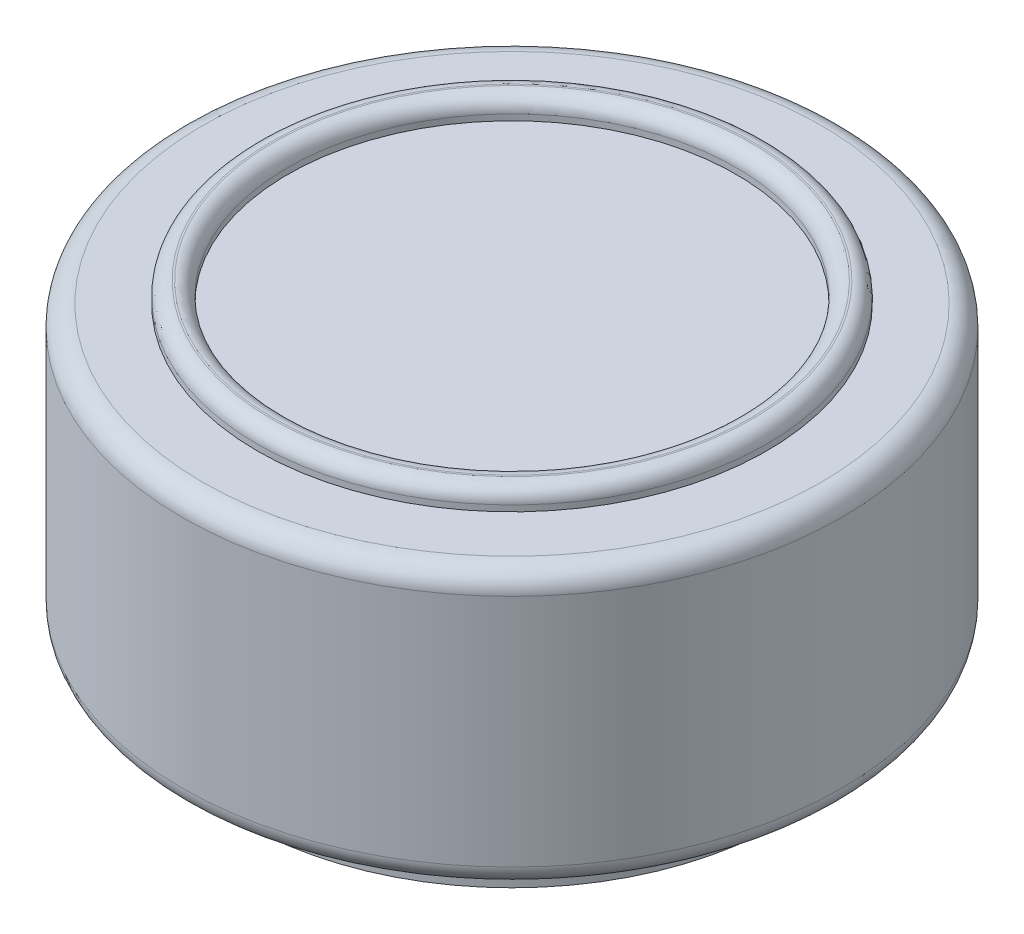
SolidWorks part; units mm, degrees
ref_plane "Front" through (0, 0, 0) normal (0, 0, 1) x (1, 0, 0)
ref_plane "Top" through (0, 0, 0) normal (0, 1, 0) x (1, 0, 0)
ref_plane "Right" through (0, 0, 0) normal (1, 0, 0) x (0, 0, -1)
sketch "Sketch1" plane through (0, 0, 0) normal (0, 1, 0) x (1, 0, 0)
  circle A0 centre (0, 0) radius 16.1655
  dimension "D1" = 32.331
extrude "Boss-Extrude1" add sketch "Sketch1" along normal blind 13.5 contours A0
fillet "Fillet1" radius 1 2 edges at (0, 0, 16.1655) (0, 13.5, 16.1655)
sketch "Sketch2" plane through (0, 13.5, 0) normal (0, 1, 0) x (1, 0, 0)
  circle A0 centre (0, 0) radius 12.5
  circle A1 centre (0, 0) radius 11
  dimension "D1" = 25
  dimension "D2" = 22
extrude "Boss-Extrude2" add sketch "Sketch2" along normal blind 1
fillet "Fillet4" radius 0.707 2 edges at (0, 14.5, 11) (0, 14.5, 12.5)
sketch "Sketch3" plane through (0, 0, 0) normal (0, -1, 0) x (1, 0, 0)
  circle A0 centre (0, 0) radius 13.1685
extrude "Boss-Extrude3" add sketch "Sketch3" along normal blind 2
